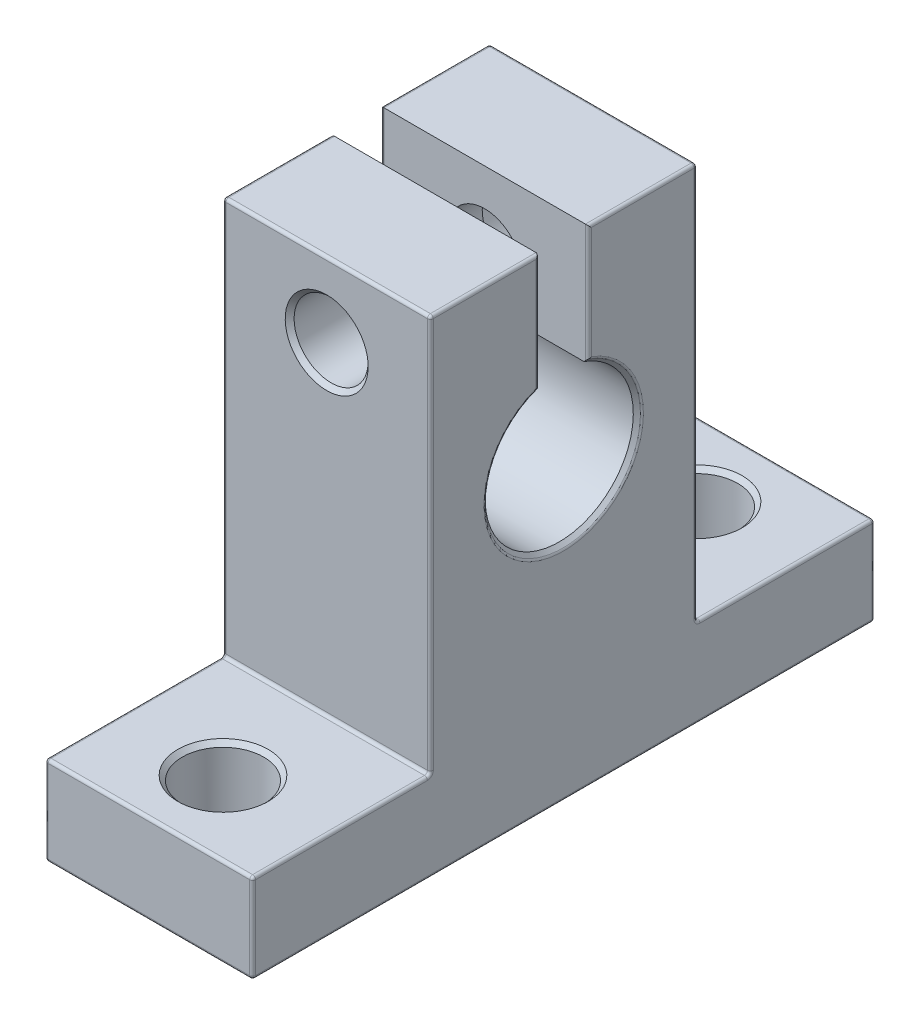
SolidWorks part; units mm, degrees
material "АМг 2 ГОСТ 4784-97"
ref_plane "Front Plane" through (0, 0, 0) normal (0, 0, 1) x (1, 0, 0)
ref_plane "Top Plane" through (0, 0, 0) normal (0, 1, 0) x (1, 0, 0)
ref_plane "Right Plane" through (0, 0, 0) normal (1, 0, 0) x (0, 0, -1)
sketch "Sketch1" plane through (0, 0, 0) normal (1, 0, 0) x (0, 0, -1)
  line L0 (-21, 0) -> (21, 0)
  line L1 (21, 0) -> (21, 6)
  line L2 (21, 6) -> (9, 6)
  line L3 (9, 6) -> (9, 32.8)
  line L4 (9, 32.8) -> (1.6667, 32.8)
  line L5 (-9, 32.8) -> (-9, 6)
  line L6 (-9, 6) -> (-21, 6)
  line L7 (-21, 6) -> (-21, 0)
  line L8 (0, 0) -> (0, 35.819) construction
  line L9 (1.6667, 24.714) -> (1.6667, 32.8)
  line L10 (-1.6667, 24.714) -> (-1.6667, 32.8)
  line L14 (-1.6667, 32.8) -> (-9, 32.8)
  arc A0 (-1.6667, 24.714) -> (1.6667, 24.714) centre (0, 20) ccw
  dimension "D8" = 10
  dimension "D1" = 42
  dimension "D2" = 32.8
  dimension "D3" = 21
  dimension "D4" = 18
  dimension "D5" = 9
  dimension "D6" = 6
  dimension "D7" = 6
  dimension "D9" = 20
  dimension "D10" = 3.3333
extrude "Boss-Extrude1" add sketch "Sketch1" along normal mid plane 14
sketch "Sketch2" plane through (0, 6, 0) normal (0, 1, 0) x (1, 0, 0)
  line L0 (7, -9) -> (7, -21) construction
  line L1 (-9.4226, 0) -> (10.9629, 0) construction
  circle A0 centre (0, 16) radius 2.75
  circle A1 centre (0, -16) radius 2.75
  dimension "D3" = 7
  dimension "D1" = 5.5
  dimension "D2" = 32
extrude "Cut-Extrude1" cut sketch "Sketch2" against normal through all
sketch "Sketch3" plane through (0, 0, -9) normal (0, 0, -1) x (-1, 0, 0)
  line L0 (-7, 32.8) -> (7, 32.8) construction
  circle A0 centre (0, 27.8) radius 2.5
  point P2 (0, 32.8)
  dimension "D1" = 5
  dimension "D2" = 5
extrude "Cut-Extrude2" cut sketch "Sketch3" against normal through all
sketch "Sketch4" plane through (0, 0, -9) normal (0, 0, -1) x (-1, 0, 0)
  circle A0 centre (0, 27.8) radius 4
  dimension "D1" = 8
extrude "Cut-Extrude3" cut sketch "Sketch4" against normal blind 5
chamfer "Фаска1" distance 0.3 angle 45 7 edges at (0, 0, -13.25) (0, 0, 18.75) (0, 30.3, 9) (-4, 27.8, -9) (0, 6, -13.25) (7, 15, 0) (0, 6, 18.75)
fillet "Скругление1" radius 0.2 32 edges at (-7, 0, 0) (-7, 3, -21) (-7, 6, -15) (-7, 19.4, -9) (-7, 32.8, -5.3333) (-7, 28.757, -1.6667) (-7, 15, 0) (-7, 28.757, 1.6667) (-7, 32.8, 5.3333) (-7, 19.4, 9) (-7, 6, 15) (-7, 3, 21) (7, 32.8, -5.3333) (7, 19.4, -9) (7, 6, -15) (7, 3, -21) (7, 0, 0) (7, 3, 21) (7, 6, 15) (7, 19.4, 9) (7, 32.8, 5.3333) (7, 28.9156, 1.6667) (7, 14.7, 0) (7, 28.9156, -1.6667) (0, 0, 21) (0, 6, 21) (0, 6, 9) (0, 32.8, 9) (0, 0, -21) (0, 32.8, -9) (0, 6, -9) (0, 6, -21)
